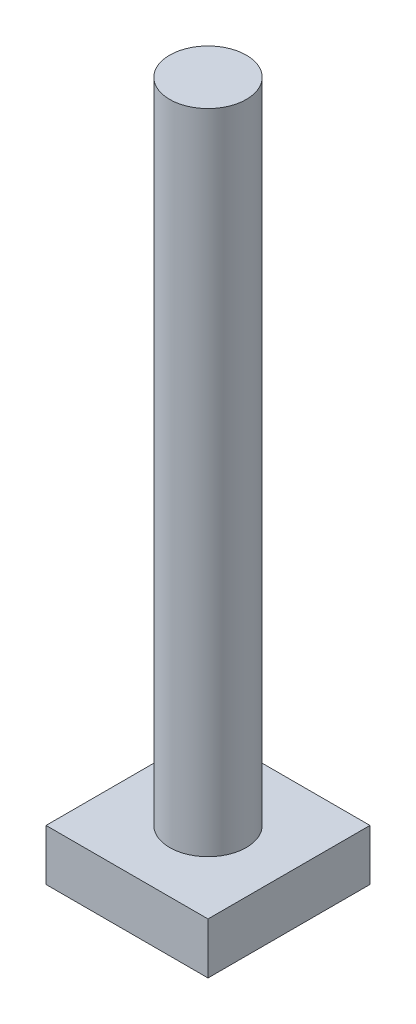
SolidWorks part; units mm, degrees
ref_plane "Front Plane" through (0, 0, 0) normal (0, 0, 1) x (1, 0, 0)
ref_plane "Top Plane" through (0, 0, 0) normal (0, 1, 0) x (1, 0, 0)
ref_plane "Right Plane" through (0, 0, 0) normal (1, 0, 0) x (0, 0, -1)
sketch "Sketch1" plane through (0, 0, 0) normal (0, 1, 0) x (1, 0, 0)
  line L1 (-9.5, -9.5) -> (9.5, -9.5)
  line L2 (-9.5, -9.5) -> (-9.5, 9.5)
  line L3 (-9.5, 9.5) -> (9.5, 9.5)
  line L4 (9.5, -9.5) -> (9.5, 9.5)
  line L5 (-9.5, -9.5) -> (9.5, 9.5) construction
  line L6 (-9.5, 9.5) -> (9.5, -9.5) construction
  point P0 (0, 0)
  dimension "D1" = 19
  dimension "D2" = 19
extrude "Boss-Extrude1" add sketch "Sketch1" along normal blind 6
sketch "Sketch2" plane through (0, 6, 0) normal (0, 1, 0) x (1, 0, 0)
  circle A0 centre (0, 0) radius 4.5
  dimension "D1" = 9
extrude "Boss-Extrude2" add sketch "Sketch2" along normal blind 76
